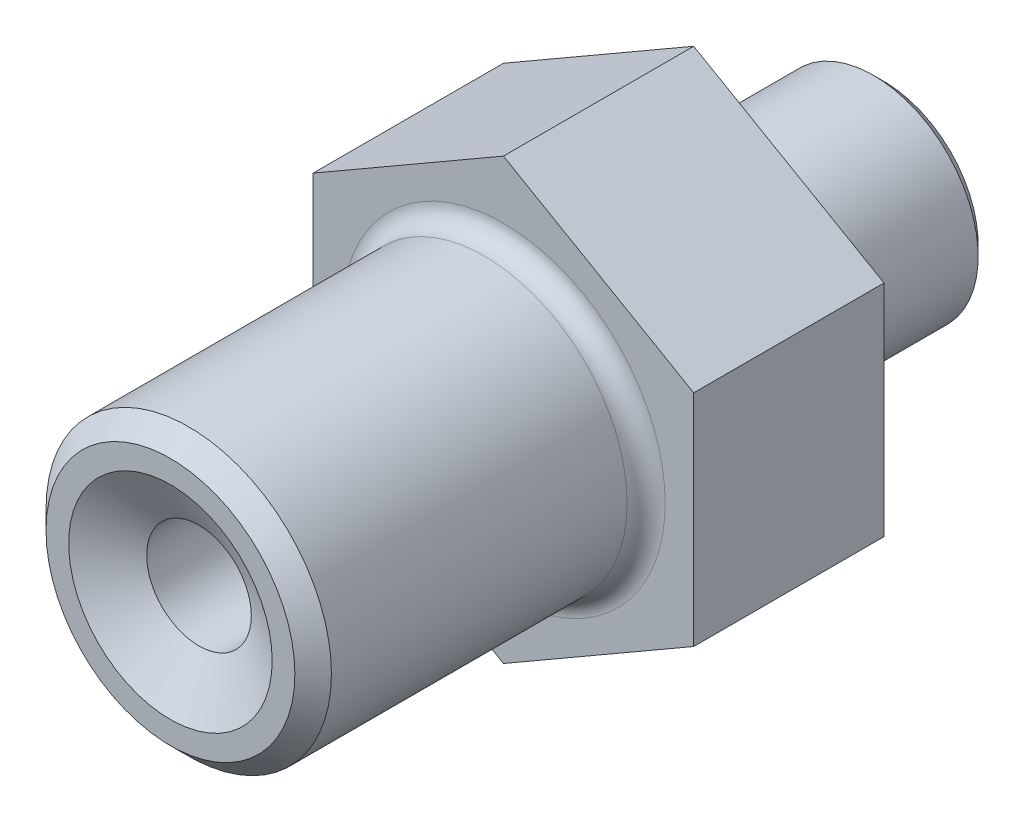
SolidWorks part; units mm, degrees
material "Сталь"
ref_plane "Спереди" through (0, 0, 0) normal (0, 0, 1) x (1, 0, 0)
ref_plane "Сверху" through (0, 0, 0) normal (0, 1, 0) x (1, 0, 0)
ref_plane "Справа" through (0, 0, 0) normal (1, 0, 0) x (0, 0, -1)
sketch "Эскиз1" plane through (0, 0, 0) normal (0, 0, 1) x (1, 0, 0)
  circle A0 centre (0, 0) radius 17.5
  dimension "D1" = 35
extrude "Бобышка-Вытянуть1" add sketch "Эскиз1" along normal blind 20
sketch "Эскиз2" plane through (0, 0, 20) normal (0, 0, 1) x (1, 0, 0)
  circle A0 centre (0, 0) radius 15
  dimension "D1" = 30
extrude "Бобышка-Вытянуть2" add sketch "Эскиз2" along normal blind 35
cosmetic thread "Условное изображение резьбы2" parameters "D1"=25, "D2"=26.158
sketch "Эскиз3" plane through (0, 0, 0) normal (0, 0, -1) x (-1, 0, 0)
  circle A0 centre (0, 0) radius 11
  dimension "D1" = 22
extrude "Бобышка-Вытянуть3" add sketch "Эскиз3" along normal blind 20
cosmetic thread "Условное изображение резьбы1" parameters "D2"=19.797
sketch "Эскиз4" plane through (0, 0, 0) normal (1, 0, 0) x (0, 0, -1)
  line L0 (-55, 0) -> (20, 0) construction
  line L1 (-55, 15) -> (-55, -15) construction
  line L2 (20, -11) -> (20, 11) construction
  line L3 (-55, 0) -> (-55, 10.6962)
  line L4 (-55, 10.6962) -> (-52, 5.5)
  line L5 (-52, 5.5) -> (20, 5.5)
  line L6 (20, 5.5) -> (20, 0)
  line L7 (-55, 0) -> (20, 0)
  dimension "D1" = 11
  dimension "D2" = 3
  dimension "D3" = 60
revolve "Вырез-Повернуть1" cut sketch "Эскиз4" angle 360 about L0
chamfer "Фаска1" distance 1.1015 angle 45 1 edges at (-11, 0, -20)
sketch "Эскиз5" plane through (0, 0, 0) normal (0, 0, -1) x (-1, 0, 0)
  circle A0 centre (0, 0) radius 9.5
  circle A1 centre (0, 0) radius 17.5
  circle A2 centre (0, 0) radius 17.5 construction
  dimension "D1" = 19
extrude "Вырез-Вытянуть1" cut sketch "Эскиз5" along normal blind 2
chamfer "Фаска2" distance 1.921 angle 45 1 edges at (15, 0, 55)
fillet "Скругление1" radius 2 1 edges at (15, 0, 20)
chamfer "Фаска3" distance 2 angle 30 1 edges at (5.5, 0, -20)
sketch "Эскиз6" plane through (0, 0, 0) normal (0, 0, -1) x (-1, 0, 0)
  line L1 (0, 23.094) -> (-20, 11.547)
  line L2 (-20, 11.547) -> (-20, -11.547)
  line L3 (-20, -11.547) -> (0, -23.094)
  line L4 (0, -23.094) -> (20, -11.547)
  line L5 (20, -11.547) -> (20, 11.547)
  line L6 (20, 11.547) -> (0, 23.094)
  circle A0 centre (0, 0) radius 20 construction
  circle A1 centre (0, 0) radius 17.5
  circle A2 centre (0, 0) radius 17.5
  dimension "D2" = 40
  dimension "D1" = 0
extrude "Бобышка-Вытянуть4" add sketch "Эскиз6" against normal up to surface (20 mm away) up to face at (17, 0, 20)
